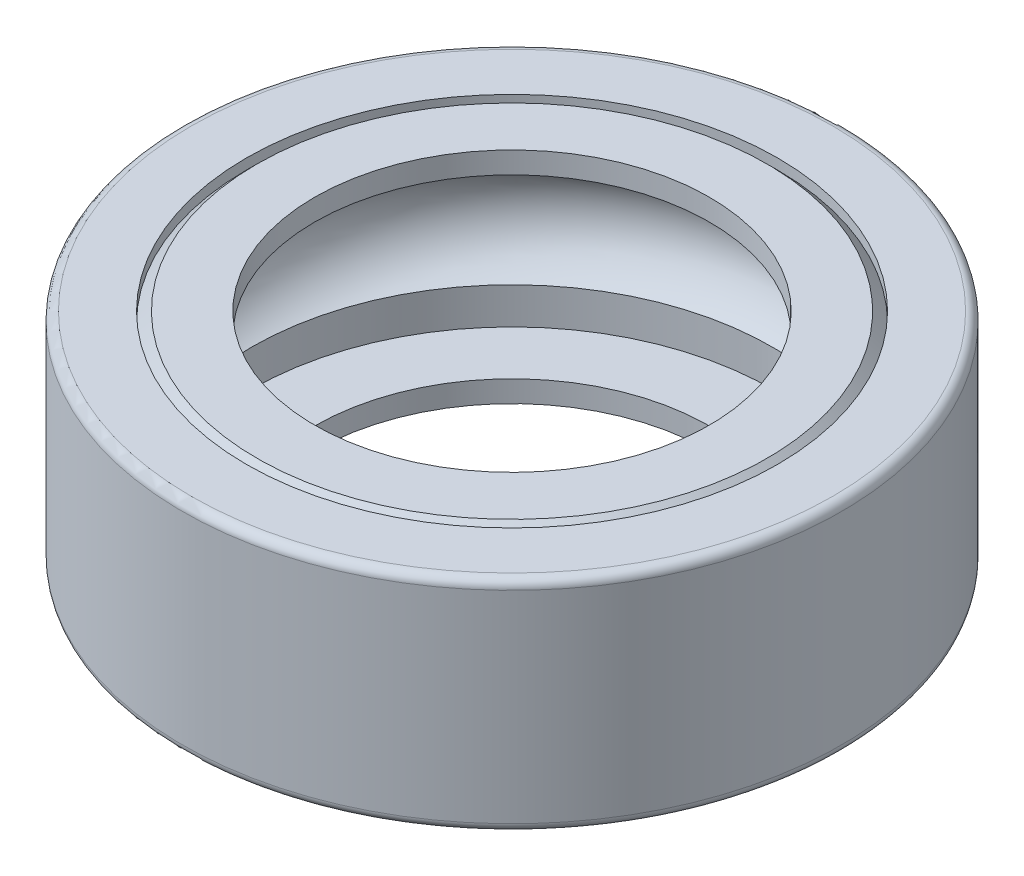
SolidWorks part; units mm, degrees
ref_plane "Front Plane" through (0, 0, 0) normal (0, 0, 1) x (1, 0, 0)
ref_plane "Top Plane" through (0, 0, 0) normal (0, 1, 0) x (1, 0, 0)
ref_plane "Right Plane" through (0, 0, 0) normal (1, 0, 0) x (0, 0, -1)
ref_plane "Plane1" through (0, 0, 0) normal (0, 0, -1) x (-1, 0, 0)
sketch "Sketch1" plane through (0, 0, 0) normal (0, 0, -1) x (-1, 0, 0)
  line L0 (-5.925, -4.5) -> (-5.925, -3.6691)
  line L1 (-5.925, -1.3309) -> (-5.925, -0.5)
  line L2 (-5.925, -0.5) -> (-6.0435, -0.5)
  line L3 (-6.0435, -0.5) -> (-6.0435, -0.49)
  line L4 (-6.0435, -0.49) -> (-4.4935, -0.49)
  line L5 (-4.4935, -0.49) -> (-4.4935, 0)
  line L6 (-4.4935, 0) -> (-5.8035, 0)
  line L7 (-5.8035, 0) -> (-6.0435, -0.24)
  line L8 (-6.0435, -0.24) -> (-6.0435, 0)
  line L9 (-6.0435, 0) -> (-7.3, 0)
  line L10 (-7.5, -0.2) -> (-7.5, -4.8)
  line L11 (-7.3, -5) -> (-6.0435, -5)
  line L12 (-6.0435, -5) -> (-6.0435, -4.76)
  line L13 (-6.0435, -4.76) -> (-5.8035, -5)
  line L14 (-5.8035, -5) -> (-4.4935, -5)
  line L15 (-4.4935, -5) -> (-4.4935, -4.51)
  line L16 (-4.4935, -4.51) -> (-6.0435, -4.51)
  line L17 (-6.0435, -4.51) -> (-6.0435, -4.5)
  line L18 (-6.0435, -4.5) -> (-5.925, -4.5)
  line L19 (0, -5.0013) -> (0, 0.0013) construction
  arc A0 (-5.925, -3.6691) -> (-5.925, -1.3309) centre (-5.25, -2.5) cw
  arc A1 (-7.3, 0) -> (-7.5, -0.2) centre (-7.3, -0.2) ccw
  arc A2 (-7.5, -4.8) -> (-7.3, -5) centre (-7.3, -4.8) ccw
revolve "Revolve1" add sketch "Sketch1" angle 360 about L19
